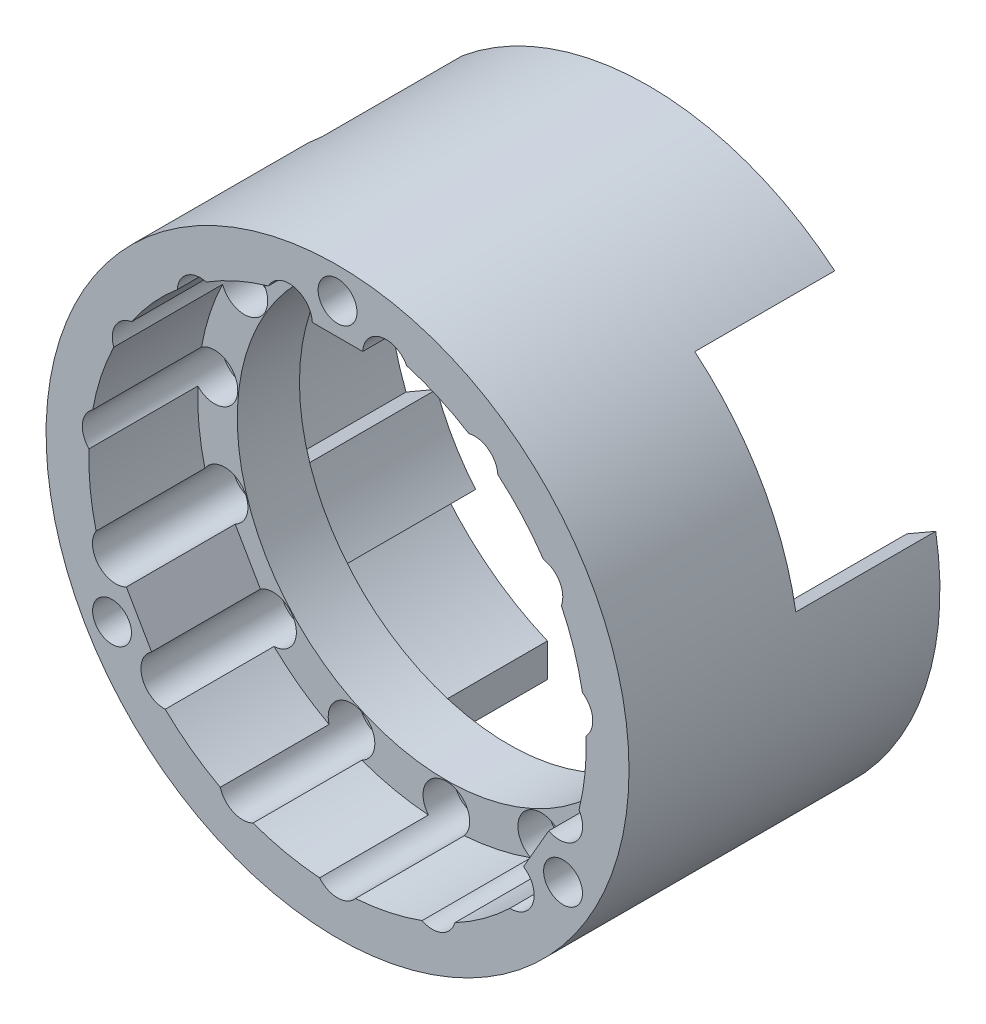
SolidWorks part; units mm, degrees
ref_plane "前视基准面" through (0, 0, 0) normal (0, 0, 1) x (1, 0, 0)
ref_plane "上视基准面" through (0, 0, 0) normal (0, 1, 0) x (1, 0, 0)
ref_plane "右视基准面" through (0, 0, 0) normal (1, 0, 0) x (0, 0, -1)
sketch "草图1" plane through (0, 0, 0) normal (0, 0, 1) x (1, 0, 0)
  circle A0 centre (0, 0) radius 18.75
  circle A3 centre (0, 16.75) radius 1.25
  circle A4 centre (14.5059, -8.375) radius 1.25
  circle A5 centre (-14.5059, -8.375) radius 1.25
  circle A6 centre (0, 0) radius 14.75
  point P12 (0, 0)
  dimension "D1" = 3
extrude "凸台-拉伸1" add sketch "草图1" along normal blind 15
sketch "草图2" plane through (0, 0, 15) normal (0, 0, 1) x (1, 0, 0)
  line L0 (-3, 14.75) -> (3, 14.75)
  line L1 (3, 14.75) -> (6.0861, 15.8732)
  line L2 (0, 0) -> (0, 5.9586)
  line L3 (-3, 14.75) -> (-6.0861, 15.8732)
  line L4 (11.2739, -9.9731) -> (10.7036, -13.2073)
  line L5 (14.2739, -4.7769) -> (11.2739, -9.9731)
  line L6 (14.2739, -4.7769) -> (16.7897, -2.6659)
  line L7 (-14.2739, -4.7769) -> (-16.7897, -2.6659)
  line L8 (-11.2739, -9.9731) -> (-14.2739, -4.7769)
  line L9 (-11.2739, -9.9731) -> (-10.7036, -13.2073)
  arc A0 (-10.7036, -13.2073) -> (10.7036, -13.2073) centre (0, 0) ccw
  circle A1 centre (0, 0) radius 14.75 construction
  arc A2 (16.7897, -2.6659) -> (6.0861, 15.8732) centre (0, 0) ccw
  arc A3 (-6.0861, 15.8732) -> (-16.7897, -2.6659) centre (0, 0) ccw
  point P10 (0, 14.75)
  point P21 (0, 0)
  circle M7 centre (0, 0) radius 14.75
  dimension "D1" = 3
extrude "切除-拉伸1" cut sketch "草图2" against normal blind 15 contours L6 A2 L1 L0 L5 M7 | L9 A0 L4 L5 L8 M7 | L3 A3 L7 L8 L0 M7
sketch "草图3" plane through (0, 0, 15) normal (0, 0, 1) x (1, 0, 0)
  line L0 (-11.2739, -9.9731) -> (-14.2739, -4.7769) construction
  line L1 (-3, 14.75) -> (3, 14.75) construction
  line L2 (14.2739, -4.7769) -> (11.2739, -9.9731) construction
  line L3 (-11.9635, -8.7786) -> (-13.5842, -5.9714)
  line L4 (-1.6207, 14.75) -> (1.6207, 14.75)
  line L5 (13.5842, -5.9714) -> (11.9635, -8.7786)
  arc A0 (1.6207, 14.75) -> (4.4467, 15.3697) centre (3.1187, 14.6722) ccw
  arc A2 (8.4465, 13.5888) -> (10.3136, 12.2323) centre (8.8168, 12.1353) ccw
  arc A3 (13.2433, 8.9785) -> (14.3973, 6.9798) centre (12.9904, 7.5) ccw
  arc A4 (15.7503, 2.8157) -> (15.9915, 0.5205) centre (14.9178, 1.5679) ccw
  arc A5 (15.5339, -3.8339) -> (13.5842, -5.9714) centre (14.2658, -4.6353) ccw
  arc A6 (11.9635, -8.7786) -> (11.0872, -11.5358) centre (11.1472, -10.037) ccw
  arc A7 (7.545, -14.1093) -> (5.4367, -15.048) centre (6.101, -13.7032) ccw
  arc A8 (1.1539, -15.9583) -> (-1.1539, -15.9583) centre (0, -15) ccw
  arc A9 (-5.4367, -15.048) -> (-7.545, -14.1093) centre (-6.101, -13.7032) ccw
  arc A10 (-11.0872, -11.5358) -> (-11.9635, -8.7786) centre (-11.1472, -10.037) ccw
  arc A11 (-13.5842, -5.9714) -> (-15.5339, -3.8339) centre (-14.2658, -4.6353) ccw
  arc A12 (-15.9915, 0.5205) -> (-15.7503, 2.8157) centre (-14.9178, 1.5679) ccw
  arc A13 (-14.3973, 6.9798) -> (-13.2433, 8.9785) centre (-12.9904, 7.5) ccw
  arc A14 (-10.3136, 12.2323) -> (-8.4465, 13.5888) centre (-8.8168, 12.1353) ccw
  arc A15 (-4.4467, 15.3697) -> (-1.6207, 14.75) centre (-3.1187, 14.6722) ccw
  arc A16 (15.5339, -3.8339) -> (15.9915, 0.5205) centre (0, 0) ccw
  circle A17 centre (0, 0) radius 18.75
  circle A18 centre (14.5059, -8.375) radius 1.25 construction
  circle A19 centre (0, 16.75) radius 1.25 construction
  circle A20 centre (-14.5059, -8.375) radius 1.25 construction
  circle A21 centre (14.5059, -8.375) radius 1.25
  circle A22 centre (0, 16.75) radius 1.25
  circle A23 centre (-14.5059, -8.375) radius 1.25
  arc A24 (7.545, -14.1093) -> (11.0872, -11.5358) centre (0, 0) ccw
  arc A25 (1.1539, -15.9583) -> (5.4367, -15.048) centre (0, 0) ccw
  arc A26 (-5.4367, -15.048) -> (-1.1539, -15.9583) centre (0, 0) ccw
  arc A27 (-11.0872, -11.5358) -> (-7.545, -14.1093) centre (0, 0) ccw
  arc A28 (-15.9915, 0.5205) -> (-15.5339, -3.8339) centre (0, 0) ccw
  arc A29 (-14.3973, 6.9798) -> (-15.7503, 2.8157) centre (0, 0) ccw
  arc A30 (-10.3136, 12.2323) -> (-13.2433, 8.9785) centre (0, 0) ccw
  arc A31 (-4.4467, 15.3697) -> (-8.4465, 13.5888) centre (0, 0) ccw
  arc A33 (8.4465, 13.5888) -> (4.4467, 15.3697) centre (0, 0) ccw
  arc A34 (13.2433, 8.9785) -> (10.3136, 12.2323) centre (0, 0) ccw
  arc A35 (15.7503, 2.8157) -> (14.3973, 6.9798) centre (0, 0) ccw
  point P35 (0, 0)
  dimension "D1" = 15
extrude "凸台-拉伸4" add sketch "草图3" along normal blind 10
sketch "草图5" plane through (0, 0, 0) normal (0, 0, 1) x (1, 0, 0)
  circle A0 centre (0, 0) radius 18.75
extrude "切除-拉伸2" cut sketch "草图5" along normal up to surface (15 mm away) up to face at (11.8893, 6.8643, 15)
sketch "草图6" plane through (0, 0, 15) normal (0, 0, -1) x (-1, 0, 0)
  circle A0 centre (3.1187, 14.6722) radius 1.5
  circle A1 centre (8.8168, 12.1353) radius 1.5
  circle A2 centre (12.9904, 7.5) radius 1.5
  circle A3 centre (14.9178, 1.5679) radius 1.5
  circle A4 centre (14.2658, -4.6353) radius 1.5
  circle A5 centre (11.1472, -10.037) radius 1.5
  circle A6 centre (6.101, -13.7032) radius 1.5
  circle A7 centre (0, -15) radius 1.5
  circle A8 centre (-6.101, -13.7032) radius 1.5
  circle A9 centre (-11.1472, -10.037) radius 1.5
  circle A10 centre (-14.2658, -4.6353) radius 1.5
  circle A11 centre (-14.9178, 1.5679) radius 1.5
  circle A12 centre (-12.9904, 7.5) radius 1.5
  circle A13 centre (-8.8168, 12.1353) radius 1.5
  circle A14 centre (-3.1187, 14.6722) radius 1.5
  point P33 (0, 0)
  dimension "D1" = 15
extrude "切除-拉伸3" cut sketch "草图6" against normal blind 10
sketch "草图7" plane through (0, 0, 15) normal (0, 0, -1) x (-1, 0, 0)
  circle A0 centre (0, 0) radius 12
  circle A1 centre (3.1187, 14.6722) radius 1.5
  circle A2 centre (8.8168, 12.1353) radius 1.5
  circle A3 centre (12.9904, 7.5) radius 1.5
  circle A4 centre (14.9178, 1.5679) radius 1.5
  circle A5 centre (14.2658, -4.6353) radius 1.5
  circle A6 centre (11.1472, -10.037) radius 1.5
  circle A7 centre (6.101, -13.7032) radius 1.5
  circle A8 centre (0, -15) radius 1.5
  circle A9 centre (-6.101, -13.7032) radius 1.5
  circle A10 centre (-11.1472, -10.037) radius 1.5
  circle A11 centre (-14.2658, -4.6353) radius 1.5
  circle A12 centre (-14.9178, 1.5679) radius 1.5
  circle A13 centre (-12.9904, 7.5) radius 1.5
  circle A14 centre (-8.8168, 12.1353) radius 1.5
  circle A15 centre (-3.1187, 14.6722) radius 1.5
  circle A17 centre (0, 0) radius 18.75
  circle A24 centre (14.5059, -8.375) radius 1.25 construction
  circle A25 centre (-14.5059, -8.375) radius 1.25 construction
  circle A26 centre (0, 16.75) radius 1.25 construction
  circle A27 centre (14.5059, -8.375) radius 1.25
  circle A28 centre (-14.5059, -8.375) radius 1.25
  circle A29 centre (0, 16.75) radius 1.25
  point P38 (0, 0)
  dimension "D1" = 15
extrude "凸台-拉伸5" add sketch "草图7" against normal blind 1
sketch "草图8" plane through (0, 0, 16) normal (0, 0, 1) x (1, 0, 0)
  circle A0 centre (0, 0) radius 13.75
sketch "草图9" plane through (0, 0, 15) normal (0, 0, -1) x (-1, 0, 0)
  circle A0 centre (0, 0) radius 18.75
  circle A1 centre (0, 0) radius 12
  circle A2 centre (14.5059, -8.375) radius 1.25 construction
  circle A3 centre (-14.5059, -8.375) radius 1.25 construction
  circle A4 centre (0, 16.75) radius 1.25 construction
  circle A5 centre (0, 16.75) radius 1.25
  circle A6 centre (-14.5059, -8.375) radius 1.25
  circle A7 centre (14.5059, -8.375) radius 1.25
extrude "凸台-拉伸6" add sketch "草图9" along normal blind 1
sketch "草图10" plane through (0, 0, 16) normal (0, 0, 1) x (1, 0, 0)
  circle A0 centre (0, 0) radius 11.5
  circle A1 centre (0, 0) radius 12 construction
  circle A2 centre (0, 0) radius 12
extrude "凸台-拉伸7" add sketch "草图10" against normal up to surface (2 mm away) up to face at (13.2559, -8.375, 14)
sketch "草图13" plane through (0, 0, 14) normal (0, 0, -1) x (-1, 0, 0)
  circle A0 centre (0, 0) radius 18.75
  circle A1 centre (0, 0) radius 11.5
  circle A2 centre (14.5059, -8.375) radius 1.25 construction
  circle A3 centre (-14.5059, -8.375) radius 1.25 construction
  circle A4 centre (0, 16.75) radius 1.25 construction
  circle A5 centre (0, 16.75) radius 1.25
  circle A6 centre (-14.5059, -8.375) radius 1.25
  circle A7 centre (14.5059, -8.375) radius 1.25
extrude "凸台-拉伸9" add sketch "草图13" along normal blind 2
sketch "草图14" plane through (0, 0, 25) normal (0, 0, 1) x (1, 0, 0)
  circle A0 centre (0, 0) radius 18.75
extrude "切除-拉伸4" cut sketch "草图14" against normal blind 2
sketch "草图15" plane through (0, 0, 12) normal (0, 0, -1) x (-1, 0, 0)
  line L0 (11.1193, -9.3065) -> (13.0934, -10.4463)
  line L1 (2.5, 14.2829) -> (2.5, 16.5624)
  line L2 (13.6193, -4.9764) -> (15.5934, -6.1161)
  line L3 (-2.5, 14.2829) -> (-2.5, 16.5624)
  line L4 (-13.6193, -4.9764) -> (-15.5934, -6.1161)
  line L5 (-11.1193, -9.3065) -> (-13.0934, -10.4463)
  arc A0 (2.5, 14.2829) -> (-2.5, 14.2829) centre (0, 0) ccw
  circle A1 centre (0, 0) radius 18.75
  arc A2 (-2.5, 16.5624) -> (-15.5934, -6.1161) centre (0, 0) ccw
  arc A3 (-13.6193, -4.9764) -> (-11.1193, -9.3065) centre (0, 0) ccw
  arc A4 (11.1193, -9.3065) -> (13.6193, -4.9764) centre (0, 0) ccw
  arc A5 (15.5934, -6.1161) -> (2.5, 16.5624) centre (0, 0) ccw
  arc A6 (-13.0934, -10.4463) -> (13.0934, -10.4463) centre (0, 0) ccw
  circle A7 centre (14.5059, -8.375) radius 1.25 construction
  circle A8 centre (0, 16.75) radius 1.25 construction
  circle A9 centre (-14.5059, -8.375) radius 1.25 construction
  circle A10 centre (14.5059, -8.375) radius 1.25
  circle A11 centre (0, 16.75) radius 1.25
  circle A12 centre (-14.5059, -8.375) radius 1.25
  point P20 (0, 0)
extrude "凸台-拉伸10" add sketch "草图15" along normal blind 9
sketch "草图16" plane through (0, 0, 3) normal (0, 0, -1) x (-1, 0, 0)
  line L0 (-16.6192, 2.0895) -> (-18.481, 3.1645)
  line L1 (6.5, -15.4374) -> (6.5, -17.5873)
  line L2 (-10.1192, 13.3479) -> (-11.981, 14.4228)
  line L3 (-6.5, -15.4374) -> (-6.5, -17.5873)
  line L4 (10.1192, 13.3479) -> (11.981, 14.4228)
  line L5 (16.6192, 2.0895) -> (18.481, 3.1645)
  circle A0 centre (0, 0) radius 18.75 construction
  arc A1 (-6.5, -17.5873) -> (6.5, -17.5873) centre (0, 0) ccw
  arc A2 (-13.0934, -10.4463) -> (13.0934, -10.4463) centre (0, 0) ccw construction
  arc A3 (-6.5, -15.4374) -> (6.5, -15.4374) centre (0, 0) ccw
  arc A4 (-11.981, 14.4228) -> (-18.481, 3.1645) centre (0, 0) ccw
  arc A5 (-10.1192, 13.3479) -> (-16.6192, 2.0895) centre (0, 0) ccw
  arc A6 (18.481, 3.1645) -> (11.981, 14.4228) centre (0, 0) ccw
  arc A7 (16.6192, 2.0895) -> (10.1192, 13.3479) centre (0, 0) ccw
  point P22 (0, 0)
extrude "切除-拉伸6" cut sketch "草图16" against normal blind 9
sketch "草图17" plane through (0, 0, 16) normal (0, 0, 1) x (1, 0, 0)
  circle A0 centre (0, 0) radius 13.45
extrude "切除-拉伸8" cut sketch "草图17" against normal blind 10
sketch "草图18" plane through (0, 0, 15) normal (0, 0, 1) x (1, 0, 0)
  circle A0 centre (11.1472, -10.037) radius 1.5 construction
  circle A1 centre (14.2658, -4.6353) radius 1.5
  circle A2 centre (14.2658, -4.6353) radius 1.5
  circle A3 centre (6.101, -13.7032) radius 1.5 construction
  circle A4 centre (0, -15) radius 1.5 construction
  circle A5 centre (-6.101, -13.7032) radius 1.5 construction
  circle A6 centre (-11.1472, -10.037) radius 1.5 construction
  circle A7 centre (-14.2658, -4.6353) radius 1.5 construction
  circle A8 centre (-14.9178, 1.5679) radius 1.5 construction
  circle A9 centre (-12.9904, 7.5) radius 1.5 construction
  circle A10 centre (-8.8168, 12.1353) radius 1.5 construction
  circle A11 centre (-3.1187, 14.6722) radius 1.5 construction
  circle A12 centre (3.1187, 14.6722) radius 1.5 construction
  circle A13 centre (8.8168, 12.1353) radius 1.5 construction
  circle A14 centre (12.9904, 7.5) radius 1.5 construction
  circle A15 centre (14.9178, 1.5679) radius 1.5 construction
  circle A16 centre (11.1472, -10.037) radius 1.5
  circle A17 centre (6.101, -13.7032) radius 1.5
  circle A18 centre (0, -15) radius 1.5
  circle A19 centre (-6.101, -13.7032) radius 1.5
  circle A20 centre (-11.1472, -10.037) radius 1.5
  circle A21 centre (-14.2658, -4.6353) radius 1.5
  circle A22 centre (-14.9178, 1.5679) radius 1.5
  circle A23 centre (-12.9904, 7.5) radius 1.5
  circle A24 centre (-8.8168, 12.1353) radius 1.5
  circle A25 centre (-3.1187, 14.6722) radius 1.5
  circle A26 centre (3.1187, 14.6722) radius 1.5
  circle A27 centre (8.8168, 12.1353) radius 1.5
  circle A28 centre (12.9904, 7.5) radius 1.5
  circle A29 centre (14.9178, 1.5679) radius 1.5
  dimension "D1" = 0
extrude "切除-拉伸9" cut sketch "草图18" against normal blind 1
